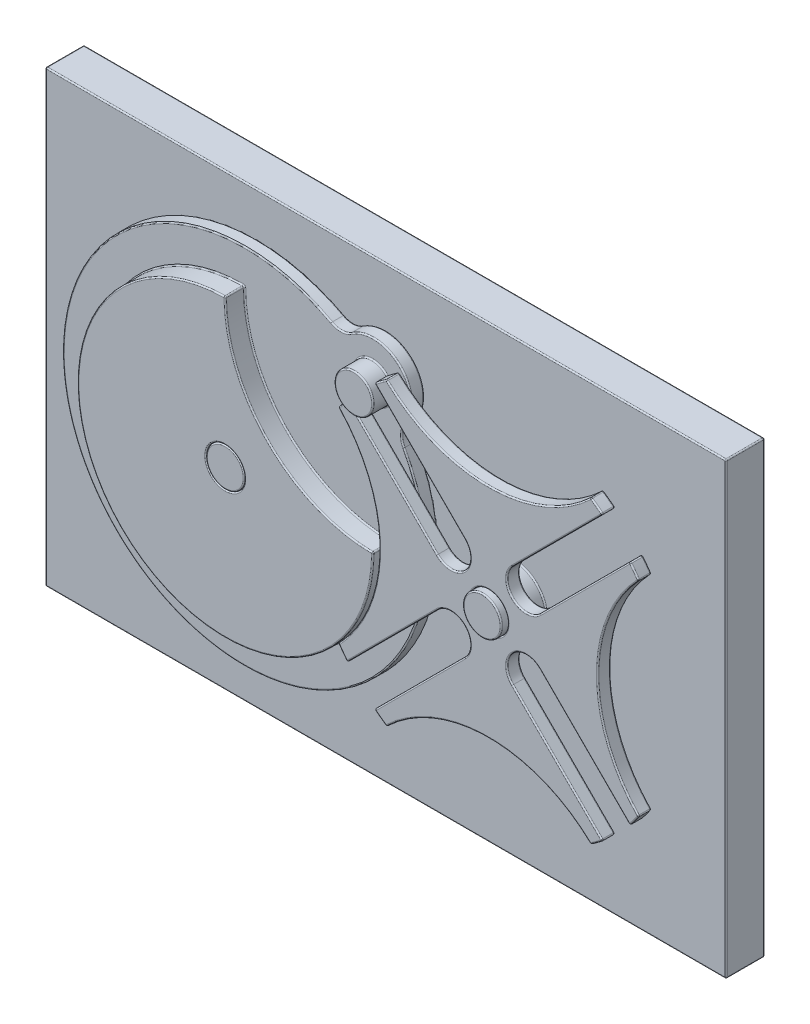
SolidWorks part; units mm, degrees
ref_plane "Front Plane" through (0, 0, 0) normal (0, 0, 1) x (1, 0, 0)
ref_plane "Top Plane" through (0, 0, 0) normal (0, 1, 0) x (1, 0, 0)
ref_plane "Right Plane" through (0, 0, 0) normal (1, 0, 0) x (0, 0, -1)
sketch "Sketch1" plane through (0, 0, 0) normal (0, 0, 1) x (1, 0, 0)
  line L0 (0, 100) -> (100, 0)
  line L1 (10.6066, 110.6066) -> (81.3173, 39.8959)
  line L3 (60.1041, 18.6827) -> (-10.6066, 89.3934)
  circle A0 centre (-100, 0) radius 141.4214
  circle A1 centre (100, 0) radius 141.4214
  circle A2 centre (0, 100) radius 15
  circle A3 centre (-100, 0) radius 115
  arc A4 (81.3173, 39.8959) -> (60.1041, 18.6827) centre (70.7107, 29.2893) cw
  dimension "D1" = 200
  dimension "D3" = 282.8427
  dimension "D4" = 30
  dimension "D5" = 230
  dimension "D6" = 100
  dimension "D2" = 100
sketch "Sketch3" plane through (0, 0, 0) normal (0, 0, 1) x (1, 0, 0)
  line L0 (60.1041, 18.6827) -> (-10.0425, 88.8293)
  line L1 (60.1041, 18.6827) -> (-10.6066, 89.3934) construction
  line L2 (100, 0) -> (25.5915, 74.4085) construction
  line L3 (0, 100) -> (100, 0) construction
  line L4 (81.3173, 39.8959) -> (11.1707, 110.0425)
  line L5 (118.6827, 39.8959) -> (188.8293, 110.0425)
  line L6 (139.8959, 18.6827) -> (210.0425, 88.8293)
  line L7 (139.8959, -18.6827) -> (210.0425, -88.8293)
  line L8 (118.6827, -39.8959) -> (188.8293, -110.0425)
  line L9 (81.3173, -39.8959) -> (11.1707, -110.0425)
  line L10 (60.1041, -18.6827) -> (-10.0425, -88.8293)
  circle A0 centre (100, 0) radius 141.4214 construction
  arc A1 (-10.0425, 88.8293) -> (-16.9375, 79.5338) centre (100, 0) ccw
  circle A2 centre (-100, 0) radius 115 construction
  arc A3 (11.1707, 110.0425) -> (20.4662, 116.9375) centre (100, 0) cw
  arc A4 (60.1041, 18.6827) -> (81.3173, 39.8959) centre (70.7107, 29.2893) ccw
  arc A5 (-16.9375, 79.5338) -> (-16.9375, -79.5338) centre (-100, 0) cw
  arc A6 (188.8293, 110.0425) -> (179.5338, 116.9375) centre (100, 0) ccw
  arc A7 (210.0425, 88.8293) -> (216.9375, 79.5338) centre (100, 0) cw
  arc A8 (118.6827, 39.8959) -> (139.8959, 18.6827) centre (129.2893, 29.2893) ccw
  arc A9 (179.5338, 116.9375) -> (20.4662, 116.9375) centre (100, 200) cw
  arc A10 (210.0425, -88.8293) -> (216.9375, -79.5338) centre (100, 0) ccw
  arc A11 (188.8293, -110.0425) -> (179.5338, -116.9375) centre (100, 0) cw
  arc A12 (139.8959, -18.6827) -> (118.6827, -39.8959) centre (129.2893, -29.2893) ccw
  arc A13 (216.9375, -79.5338) -> (216.9375, 79.5338) centre (300, 0) cw
  arc A14 (11.1707, -110.0425) -> (20.4662, -116.9375) centre (100, 0) ccw
  arc A15 (-10.0425, -88.8293) -> (-16.9375, -79.5338) centre (100, 0) cw
  arc A16 (81.3173, -39.8959) -> (60.1041, -18.6827) centre (70.7107, -29.2893) ccw
  arc A17 (20.4662, -116.9375) -> (179.5338, -116.9375) centre (100, -200) cw
  dimension "D1" = 4
extrude "Boss-Extrude2" add sketch "Sketch3" along normal blind 10
sketch "Sketch4" plane through (0, 0, 0) normal (0, 0, 1) x (1, 0, 0)
  circle A0 centre (-100, 0) radius 141.4214 construction
  arc A1 (-32.3022, 124.1652) -> (24.1652, 67.6978) centre (-100, 0) ccw
  arc A2 (24.89, 83.2522) -> (-16.7478, 124.89) centre (0, 100) ccw
  circle A3 centre (0, 100) radius 15 construction
  arc A4 (24.89, 83.2522) -> (24.1652, 67.6978) centre (37.3349, 74.8783) ccw
  arc A5 (-16.7478, 124.89) -> (-32.3022, 124.1652) centre (-25.1217, 137.3349) cw
  dimension "D1" = 15
  dimension "D2" = 15
extrude "Boss-Extrude3" add sketch "Sketch4" against normal blind 10 separate body
sketch "Sketch5" plane through (0, 0, 0) normal (0, 0, 1) x (1, 0, 0)
  circle A0 centre (0, 100) radius 15 construction
  circle A1 centre (0, 100) radius 15
  circle A2 centre (-100, 0) radius 115 construction
  arc A3 (-100, 115) -> (15, 0) centre (-100, 0) ccw
  arc A4 (15, 0) -> (-100, 115) centre (15, 115) cw
extrude "Boss-Extrude4" add sketch "Sketch5" along normal blind 15
sketch "Sketch6" plane through (0, 0, 0) normal (0, 0, 1) x (1, 0, 0)
  circle A0 centre (-100, 0) radius 15
  circle A1 centre (100, 0) radius 15
  dimension "D1" = 30
extrude "Cut-Extrude1" cut sketch "Sketch6" against normal through all and the other way through all
sketch "Sketch7" plane through (0, 0, -10) normal (0, 0, 1) x (1, 0, 0)
  line L1 (-265, 175) -> (265, 175)
  line L2 (-265, 175) -> (-265, -175)
  line L3 (-265, -175) -> (265, -175)
  line L4 (265, 175) -> (265, -175)
  line L5 (-265, 175) -> (265, -175) construction
  line L6 (-265, -175) -> (265, 175) construction
  point P0 (0, 0)
  dimension "D1" = 350
  dimension "D2" = 530
extrude "Boss-Extrude9" add sketch "Sketch7" against normal blind 30 separate body
sketch "Sketch8" plane through (0, 0, -10) normal (0, 0, 1) x (1, 0, 0)
  circle A0 centre (-100, 0) radius 15 construction
  circle A1 centre (100, 0) radius 15 construction
  circle A2 centre (-100, 0) radius 15
  circle A3 centre (100, 0) radius 15
extrude "Boss-Extrude10" add sketch "Sketch8" along normal up to surface (25 mm away) up to face at (-85, 0, 15)
sketch "Sketch9" plane through (0, 0, -10) normal (0, 0, 1) x (1, 0, 0)
  circle A0 centre (100, 0) radius 25
  circle A2 centre (100, 0) radius 15 construction
  dimension "D1" = 50
extrude "Boss-Extrude11" add sketch "Sketch9" along normal up to surface (10 mm away) up to face at (115, 0, 0)
fillet "Fillet3" radius 1 66 edges at (115, 0, 0) (25.0308, 53.756, 0) (-13.5851, 84.2521, 0) (15, 0, 0) (-13.5851, -84.2521, 0) (25.0308, -53.756, 0) (81.3173, -18.6827, 0) (46.244, -74.9692, 0) (15.7479, -113.5851, 0) (100, -85, 0) (184.2521, -113.5851, 0) (153.756, -74.9692, 0) (118.6827, -18.6827, 0) (174.9692, -53.756, 0) (213.5851, -84.2521, 0) (185, 0, 0) (213.5851, 84.2521, 0) (174.9692, 53.756, 0) (118.6827, 18.6827, 0) (153.756, 74.9692, 0) (184.2521, 113.5851, 0) (100, 85, 0) (15.7479, 113.5851, 0) (46.244, 74.9692, 0) (81.3173, 18.6827, 0) (115, 0, 10) (81.3173, 18.6827, 10) (25.0308, 53.756, 10) (-13.5851, 84.2521, 10) (15, 0, 10) (-13.5851, -84.2521, 10) (25.0308, -53.756, 10) (81.3173, -18.6827, 10) (46.244, -74.9692, 10) (15.7479, -113.5851, 10) (100, -85, 10) (184.2521, -113.5851, 10) (153.756, -74.9692, 10) (118.6827, -18.6827, 10) (174.9692, -53.756, 10) (213.5851, -84.2521, 10) (185, 0, 10) (213.5851, 84.2521, 10) (174.9692, 53.756, 10) (153.756, 74.9692, 10) (184.2521, 113.5851, 10) (100, 85, 10) (15.7479, 113.5851, 10) (46.244, 74.9692, 10) (11.1707, 110.0425, 5) (20.4662, 116.9375, 5) (179.5338, 116.9375, 5) (188.8293, 110.0425, 5) (210.0425, 88.8293, 5) (216.9375, 79.5338, 5) (216.9375, -79.5338, 5) (210.0425, -88.8293, 5) (188.8293, -110.0425, 5) (179.5338, -116.9375, 5) (20.4662, -116.9375, 5) (11.1707, -110.0425, 5) (-10.0425, -88.8293, 5) (-16.9375, -79.5338, 5) (-16.9375, 79.5338, 5) (-10.0425, 88.8293, 5) (118.6827, 18.6827, 10)
fillet "Fillet4" radius 1 18 edges at (-200, -100, 0) (-24.4236, 122.3512, 0) (21.2132, 121.2132, 0) (22.3512, 75.5764, 0) (-85, 0, 15) (-181.3173, -81.3173, 15) (-66.3173, 33.6827, 15) (-85, 0, -10) (-100, 115, 7.5) (15, 0, 7.5) (15, 100, 15) (22.3512, 75.5764, -10) (21.2132, 121.2132, -10) (-24.4236, 122.3512, -10) (-200, -100, -10) (-181.3173, -81.3173, 0) (15, 100, 0) (-66.3173, 33.6827, 0)
fillet "Fillet5" radius 1 16 edges at (0, 175, -40) (-265, 0, -40) (0, -175, -40) (265, 0, -40) (85, 0, 15) (-115, 0, 15) (125, 0, -10) (-85, 0, -10) (0, -175, -10) (-265, 0, -10) (0, 175, -10) (265, 0, -10) (265, -175, -25) (-265, -175, -25) (-265, 175, -25) (265, 175, -25)
split "Split1" bodies to split 105 112 106 resulting bodies 109 110 111
